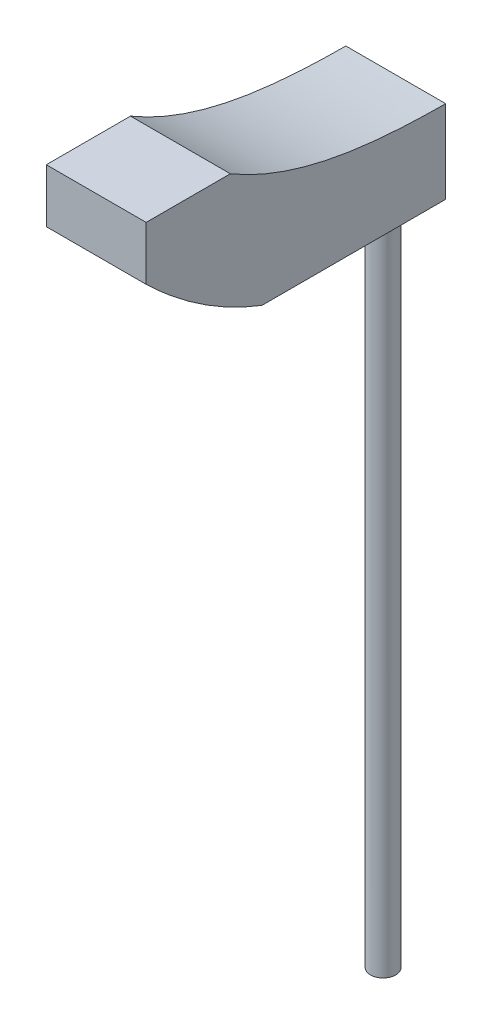
SolidWorks part; units mm, degrees
ref_plane "Front Plane" through (0, 0, 0) normal (0, 0, 1) x (1, 0, 0)
ref_plane "Top Plane" through (0, 0, 0) normal (0, 1, 0) x (1, 0, 0)
ref_plane "Right Plane" through (0, 0, 0) normal (1, 0, 0) x (0, 0, -1)
sketch "Sketch1" plane through (0, 0, 0) normal (0, 1, 0) x (1, 0, 0)
  circle A0 centre (0, 0) radius 12.7
  dimension "D1" = 25.4
extrude "Boss-Extrude1" add sketch "Sketch1" along normal blind 815 contours A0
sketch "Sketch2" plane through (0, 0, 0) normal (0, -1, 0) x (1, 0, 0)
  point P0 (0, 0)
sketch "Sketch3" plane through (0, 815, 0) normal (0, 1, 0) x (1, 0, 0)
  line L0 (0, 12.7) -> (-50, 12.7)
  line L1 (-50, 12.7) -> (-50, -287.3)
  line L2 (-50, -287.3) -> (50, -287.3)
  line L3 (50, -287.3) -> (50, 12.7)
  line L4 (50, 12.7) -> (0, 12.7)
  circle A0 centre (0, 0) radius 12.7 construction
  dimension "D1" = 50
  dimension "D2" = 50
  dimension "D3" = 300
extrude "Boss-Extrude2" add sketch "Sketch3" against normal blind 130
sketch "Sketch5" plane through (50, 0, 0) normal (1, 0, 0) x (0, 0, -1)
  line L0 (-287.3, 815) -> (12.7, 815) construction
  line L1 (12.7, 685) -> (12.7, 815) construction
  line L2 (-202.9787, 815) -> (-272.8628, 879.499)
  line L3 (-272.8628, 879.499) -> (20.7966, 879.499)
  line L4 (20.7966, 879.499) -> (67.4029, 768.4903)
  line L5 (-301.6985, 775.8323) -> (-354.1953, 601.7646)
  line L6 (-354.1953, 601.7646) -> (-151.0629, 574.8185)
  line L7 (-151.0629, 574.8185) -> (-63.7927, 665.7421)
  spline S0 degree 3 poles (-202.9787, 815) (-120.4131, 766.1202) (-24.4848, 766.7615) (67.4029, 768.4903) knots 0 0 0 0 1 1 1 1
  spline S1 degree 2 poles (-301.6985, 775.8323) (-196.773, 664.7974) (-63.7927, 665.7421) knots 0 0 0 1 1 1
extrude "Cut-Extrude1" cut sketch "Sketch5" against normal through all
sketch "Sketch6" plane through (0, 685, 0) normal (0, -1, 0) x (1, 0, 0)
  circle A0 centre (0, 0) radius 12.7 construction
  circle A1 centre (0, 0) radius 12.7
  point P4 (0, 0)
